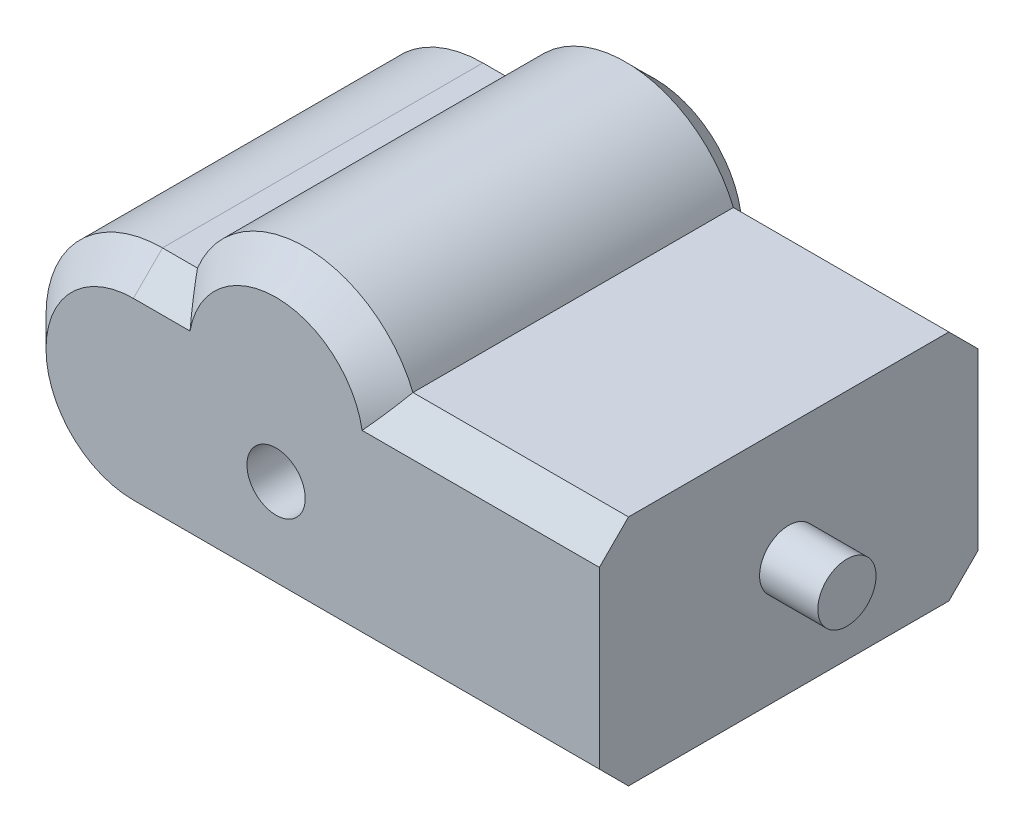
SolidWorks part; units mm, degrees
ref_plane "Front Plane" through (0, 0, 0) normal (0, 0, 1) x (1, 0, 0)
ref_plane "Top Plane" through (0, 0, 0) normal (0, 1, 0) x (1, 0, 0)
ref_plane "Right Plane" through (0, 0, 0) normal (1, 0, 0) x (0, 0, -1)
sketch "Sketch1" plane through (0, 0, 0) normal (0, 0, 1) x (1, 0, 0)
  line L1 (47.4286, 0) -> (47.4286, -40)
  line L2 (47.4286, -40) -> (-32.5714, -40)
  line L3 (-32.5714, 0) -> (-26.5714, 0)
  line L4 (10.4286, 0) -> (47.4286, 0)
  arc A0 (-32.5714, -40) -> (-32.5714, 0) centre (-32.5714, -20) cw
  arc A1 (-26.5714, 0) -> (10.4286, 0) centre (-8.0714, -7.5993) cw
  dimension "D1" = 20
  dimension "D2" = 40
  dimension "D3" = 37
  dimension "D4" = 37
  dimension "D5" = 6
extrude "Boss-Extrude1" add sketch "Sketch1" along normal mid plane 65
chamfer "Chamfer1" distance 5 angle 45 10 edges at (7.4286, -40, -32.5) (-52.5714, -20, -32.5) (-29.5714, 0, -32.5) (-8.0714, 12.4007, -32.5) (28.9286, 0, -32.5) (7.4286, -40, 32.5) (-52.5714, -20, 32.5) (-29.5714, 0, 32.5) (-8.0714, 12.4007, 32.5) (28.9286, 0, 32.5)
sketch "Sketch2" plane through (0, 0, 32.5) normal (0, 0, 1) x (1, 0, 0)
  line L0 (-32.5714, 0) -> (-26.5714, 0) construction
  circle A0 centre (-8.0714, -20) radius 5
  dimension "D1" = 10
  dimension "D2" = 20
  dimension "D3" = 18.5
extrude "Cut-Extrude1" cut sketch "Sketch2" against normal blind 10
sketch "Sketch3" plane through (47.4286, 0, 0) normal (1, 0, 0) x (0, 0, -1)
  line L0 (32.5, -35) -> (32.5, -5) construction
  circle A0 centre (0, -20) radius 5
  point P2 (0, 0)
  point P5 (32.5, -20)
  dimension "D1" = 10
extrude "Boss-Extrude2" add sketch "Sketch3" along normal blind 10
